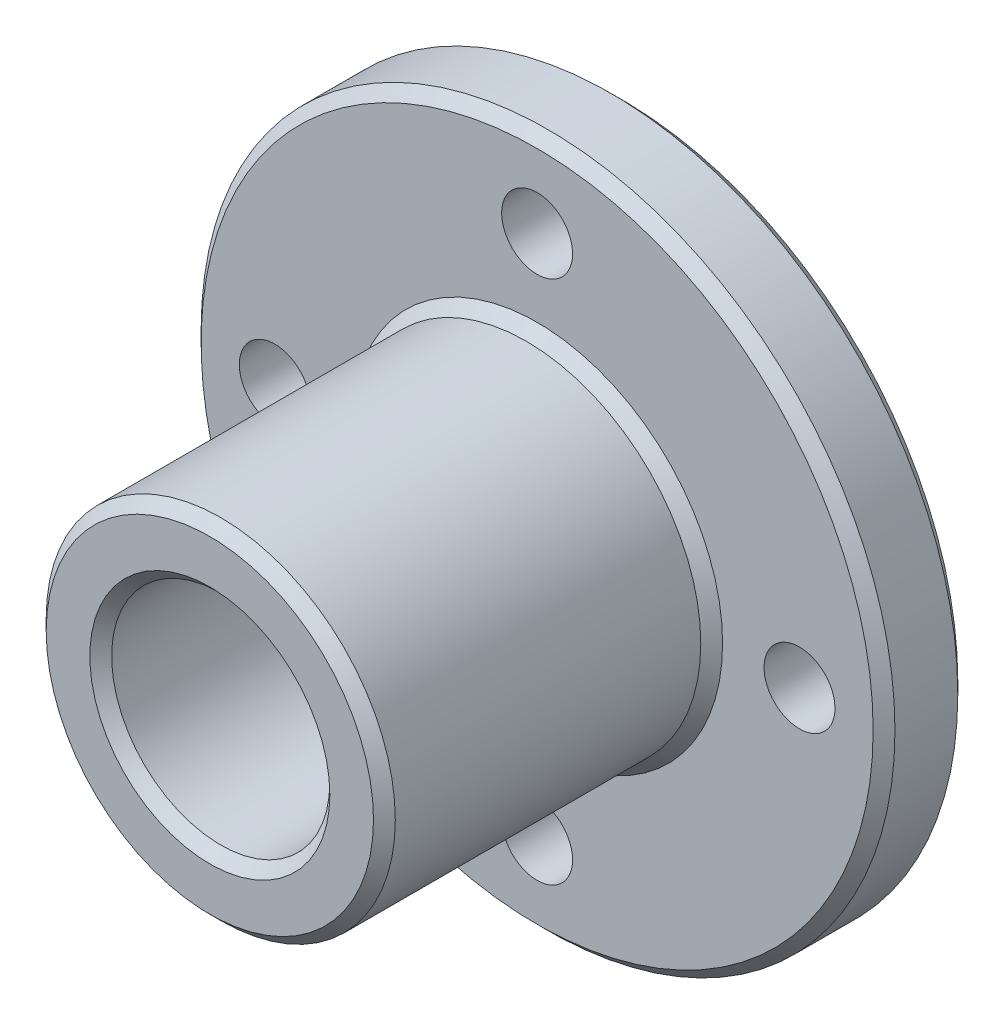
SolidWorks part; units mm, degrees
material "Brass"
ref_plane "Front Plane" through (0, 0, 0) normal (0, 0, 1) x (1, 0, 0)
ref_plane "Top Plane" through (0, 0, 0) normal (0, 1, 0) x (1, 0, 0)
ref_plane "Right Plane" through (0, 0, 0) normal (1, 0, 0) x (0, 0, -1)
sketch "Sketch1" plane through (0, 0, 0) normal (0, 0, 1) x (1, 0, 0)
  circle A0 centre (0, 0) radius 15.9
  circle A1 centre (0, 0) radius 8 construction
  circle A2 centre (0, 0) radius 5
  circle A3 centre (0, 0) radius 12.025 construction
  circle A4 centre (0, 12.025) radius 1.625
  circle A5 centre (12.025, 0) radius 1.625
  circle A6 centre (0, -12.025) radius 1.625
  circle A7 centre (-12.025, 0) radius 1.625
  point P14 (13.65, 0)
  point P15 (15.9, 0)
  dimension "D1" = 31.8
  dimension "D2" = 16
  dimension "D3" = 10
  dimension "D4" = 3.25
  dimension "D5" = 24.05
extrude "Boss-Extrude1" add sketch "Sketch1" along normal blind 3.88 contours A0
sketch "Sketch2" plane through (0, 0, 3.88) normal (0, 0, 1) x (1, 0, 0)
  circle A0 centre (0, 0) radius 8
  circle A1 centre (0, 0) radius 5 construction
  circle A2 centre (0, 0) radius 5
  dimension "D1" = 16
extrude "Boss-Extrude2" add sketch "Sketch2" along normal blind 15
chamfer "Chamfer1" distance 0.5 angle 45 5 edges at (8, 0, 18.88) (5, 0, 18.88) (8, 0, 3.88) (15.9, 0, 0) (15.9, 0, 3.88)
